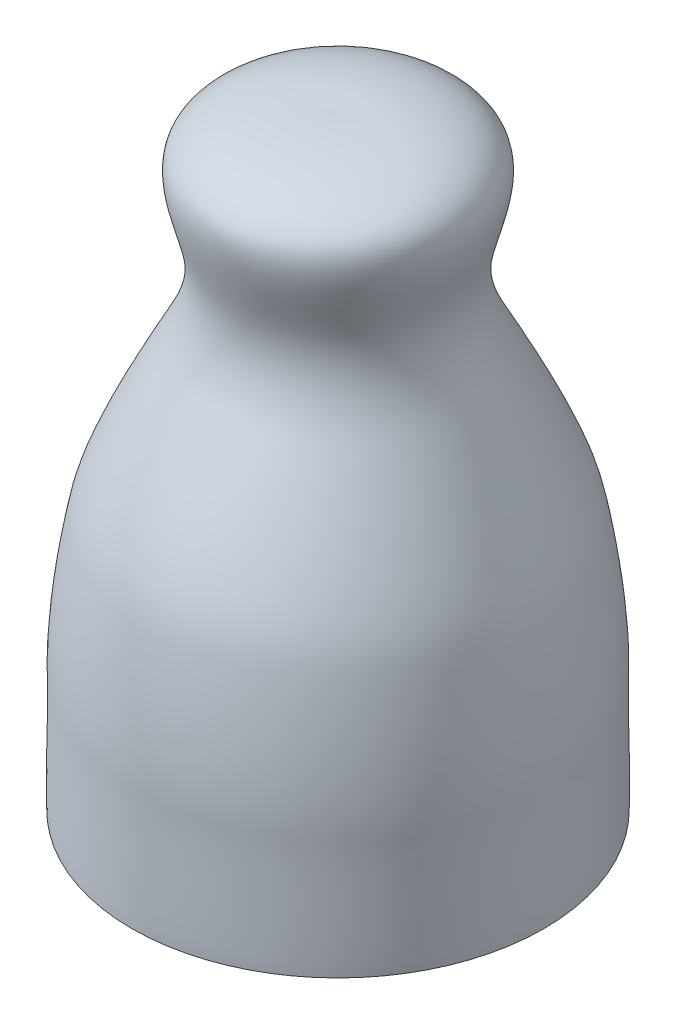
SolidWorks part; units mm, degrees
ref_plane "Front Plane" through (0, 0, 0) normal (0, 0, 1) x (1, 0, 0)
ref_plane "Top Plane" through (0, 0, 0) normal (0, 1, 0) x (1, 0, 0)
ref_plane "Right Plane" through (0, 0, 0) normal (1, 0, 0) x (0, 0, -1)
sketch "Sketch2" plane through (0, 0, 0) normal (0, 0, 1) x (1, 0, 0)
  line L2 (0, 100) -> (0, 0)
  line L3 (0, 0) -> (34, 0)
  spline S0 degree 3 poles (34, 0) (34.1456, 3.5549) (33.8158, 15.5114) (34.1491, 25.8687) (32.6587, 36.7537) (30.23, 48.5392) (21.6389, 65.7019) (19.2616, 69.7371) (16.3382, 79.7631) (25.976, 98.8057) (5.6901, 100.4978) (0, 100) knots 0 0 0 0 0.08443 0.11453 0.280281 0.317518 0.466181 0.574764 0.675979 0.807631 1 1 1 1
  dimension "D1" = 34
  dimension "D2" = 100
revolve "Revolve1" add sketch "Sketch2" angle 360 about L2
